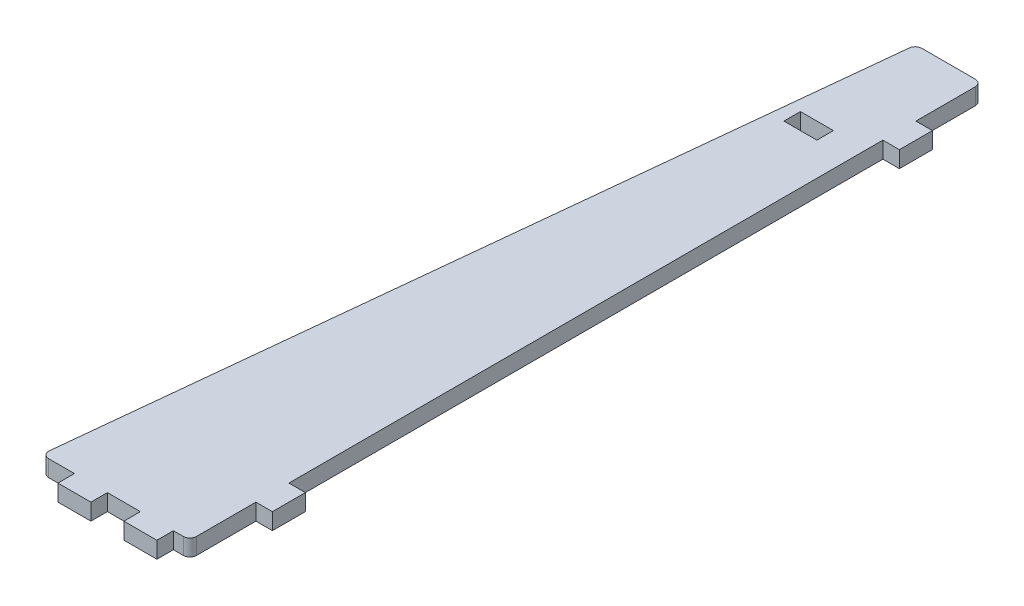
SolidWorks part; units mm, degrees
material "Beech"
ref_plane "Front Plane" through (0, 0, 0) normal (0, 0, 1) x (1, 0, 0)
ref_plane "Top Plane" through (0, 0, 0) normal (0, 1, 0) x (1, 0, 0)
ref_plane "Right Plane" through (0, 0, 0) normal (1, 0, 0) x (0, 0, -1)
sketch "Sketch1" plane through (0, 0, 0) normal (0, 1, 0) x (1, 0, 0)
  line L0 (0, 0) -> (12.7, 0)
  line L1 (12.7, 0) -> (12.7, -6.35)
  line L2 (12.7, -6.35) -> (25.4, -6.35)
  line L3 (25.4, -6.35) -> (25.4, 0)
  line L4 (25.4, 0) -> (38.1, 0)
  line L5 (38.1, 0) -> (38.1, -6.35)
  line L6 (38.1, -6.35) -> (50.8, -6.35)
  line L7 (50.8, -6.35) -> (50.8, 0)
  line L8 (50.8, 0) -> (57.15, 0)
  line L9 (57.15, 0) -> (57.15, 25.4)
  line L10 (57.15, 304.8) -> (31.75, 304.8)
  line L11 (31.75, 304.8) -> (0, 0)
  line L12 (57.15, 25.4) -> (63.5, 25.4)
  line L13 (63.5, 25.4) -> (63.5, 38.1)
  line L14 (63.5, 38.1) -> (57.15, 38.1)
  line L15 (57.15, 38.1) -> (57.15, 266.7)
  line L16 (57.15, 266.7) -> (63.5, 266.7)
  line L17 (63.5, 266.7) -> (63.5, 279.4)
  line L18 (63.5, 279.4) -> (57.15, 279.4)
  line L19 (57.15, 279.4) -> (57.15, 304.8)
  line L20 (31.75, 260.35) -> (31.75, 254)
  line L21 (31.75, 260.35) -> (44.45, 260.35)
  line L22 (31.75, 254) -> (44.45, 254)
  line L23 (44.45, 260.35) -> (44.45, 254)
  dimension "D1" = 12.7
  dimension "D2" = 6.35
  dimension "D3" = 25.4
  dimension "D4" = 25.4
  dimension "D5" = 12.7
  dimension "D6" = 304.8
  dimension "D7" = 25.4
  dimension "D8" = 25.4
  dimension "D9" = 6.35
  dimension "D10" = 254
  dimension "D11" = 6.35
  dimension "D12" = 12.7
  dimension "D13" = 12.7
extrude "Boss-Extrude1" add sketch "Sketch1" along normal blind 6.35
fillet "Fillet1" radius 2.54 4 edges at (57.15, 3.175, 0) (57.15, 3.175, -304.8) (31.75, 3.175, -304.8) (0, 3.175, 0)
equation "\"CageLeftBottomEdge\"=22.11mm"
equation "\"CageLeftTopEdge\"=22.11mm"
equation "\"CageRightBottomEdge\"=21.63mm"
equation "\"CageRightTopEdge\"=21.63mm"
equation "\"CageHeight\"=86.04mm"
equation "\"CageLength\"=73.76mm"
equation "\"CageTopScrewClearance\"=10mm"
equation "\"CageBottomScrewClearance\"=25mm"
equation "\"CageLeftTopDepth\"= 11.65mm"
equation "\"CageLeftBottomDepth\"=11.11mm"
equation "\"CageLeftTopHeight\"=8.56175mm"
equation "\"CageLeftBottomHeight\"=16mm"
equation "\"CageRightTopDepth\"= 11.05mm"
equation "\"CageRightBottomDepth\"=10.58mm"
equation "\"CageRightTopHeight\"=9.6mm"
equation "\"CageRightBottomHeight\"=15.49mm"
equation "\"CageLeftTopChannelDepth\"=2.41908mm"
equation "\"CageLeftBottomChannelDepth\"=2.588mm"
equation "\"CageLeftChannelHeight\"=11.7mm"
equation "\"CageRightTopChannelDepth\"=2.32mm"
equation "\"CageRightBottomChannelDepth\"=2.318mm"
equation "\"CageRightChannelHeight\"=10mm"
equation "\"CageChanRelHeight\"=23.99mm"
equation "\"CageChanRelDepth\"=5.492mm"
equation "\"CageChamberRadius\"=16.261mm"
equation "\"CageScrewDiameter\"=4.8mm"
equation "\"CageSetScrewDiameter\"=3.5mm"
equation "\"CageAxleRadius\"=6.639mm"
equation "\"CageAxleKeyHeight\"=1.619mm"
equation "\"CageAxleKeyWidth\"=2.662mm"
equation "\"CageHoseWindowWidth\"=16.29mm"
equation "\"CageHoseWindowHeight\"=26.5mm"
equation "\"CageHoseWindow-Edge\"=8.89mm"
equation "\"CageScrew-VerticalEdge\"=5.0mm"
equation "\"CageScrew-HorizontalEdge\"=7.5mm"
equation "\"CageScrew-HoseCornerScrewEdge\"=4.45mm"
equation "\"CageAxle-BottomEdge\"=56.05mm"
equation "\"CageAxle-FrontEdge\"=46.03mm"
equation "\"CageBackSetScrew-Axle\"=40mm"
equation "\"CageFrontSetScrew-Axle\"=22mm"
equation "\"CageVelocityWindow-BackEdge\"=34.8mm"
equation "\"CageVelocityWindow-BottomEdge\"=27.55mm"
equation "\"CageVelocityWindowHeight\"=22.29mm"
equation "\"CageVelocityWindowWidth\"=12.61mm"
equation "\"TriggerSlot-BottomEdge\"=6.35mm"
equation "\"TriggerSlot-FrontEdge\"=15mm"
equation "\"TriggerSlotSize\"=6.7mm"
equation "\"TriggerRackOffset\"=.236224in"
equation "\"TriggerSlotSizeInt\"=.25in"
equation "\"MotorMountLegLength\"=.25in"
equation "\"GearOffset\"=.264907in"
equation "\"TriggerSlotSpacing\"=.25in"
equation "\"TriggerMiniSlotWidth\"=3.5mm"
equation "\"TriggerRackWidth\"=6.5mm"
equation "\"TGMGearFaceDiameter\"=24.40mm"
equation "\"TGMCylinderLength\"=15.00mm"
equation "\"TGMScrewHole-Center\"=8.70mm"
equation "\"TGMScrewHoleDiameter\"=5.04mm"
equation "\"TGMCenterHoleDiameter\"=9.50mm"
equation "\"TGMShaftCollarSideLength\"=19.00mm"
equation "\"TGMShaftCollarDockingDepth\"=7.00mm"
equation "\"whitemotordepth\"=11.27mm"
equation "\"whitemotorbackdepth\"=3.845mm"
equation "\"whitemotoraxledepth\" = 3.5mm"
equation "\"whitemotoraxleoffset\"=11.4mm"
equation "\"whitemotorwidth\"=12.07mm"
equation "\"whitemotorheight\"=16.68mm"
equation "\"whitemotorcylinderlength\" =13.04mm"
equation "\"whitemotorcylinderradius\"=3.845mm"
equation "\"whitemotorcylinderoffset\"=2.35mm"
equation "\"whitemotorcutoutlength\"=1.88mm"
equation "\"whitemotorouterrad\"=5mm"
equation "\"whitemotorinnerrad\"=2.95mm"
equation "\"elasticracklength\"=2in"
equation "\"elasticrackpegsize\"=.25in"
equation "\"elasticrackpegbuffer\"=.125in"
equation "\"elasticrackpegspacing\"=1.76476378in"
equation "\"elasticbaybuffer\"=.25in"
equation "\"elasticdepth\"=.125in"
equation "\"elasticbaydepth\"=.75in"
equation "\"motormountwidth\"=12mm"
equation "\"motormountcornerfillet\"=3mm"
equation "\"pandiscradius\"=14in"
equation "\"towermaterialwidth\"=.25in"
equation "\"towerslotlength\"=.5in"
equation "\"towermarkerspace\"=5in"
equation "\"towerslothorizoffset\"=1in"
equation "\"towerslothorizspacing\"=2in"
equation "\"towerslotvertoffset\"=3in"
equation "\"D1@Sketch1\"=\"towerslotlength\""
equation "\"D2@Sketch1\"=\"towermaterialwidth\""
equation "\"towerupslot\"=1in"
equation "\"D3@Sketch1\"=\"towerupslot\""
equation "\"towerslotvertspacing\"=1in"
equation "\"D4@Sketch1\"=\"towerslotvertspacing\""
equation "\"D5@Sketch1\"=\"towerslotlength\""
equation "\"towerheight\"=12in"
equation "\"D6@Sketch1\"=\"towerheight\""
equation "\"D7@Sketch1\"=\"towerslotlength\"*2"
equation "\"D8@Sketch1\"=\"towerupslot\""
equation "\"D9@Sketch1\"=\"towerslotvertoffset\"-(\"towermarkerspace\"/2)-\"towermaterialwidth\""
equation "\"towermotorpanelheight\"=10in"
equation "\"D10@Sketch1\"=\"towermotorpanelheight\""
equation "\"D11@Sketch1\"=\"towermaterialwidth\""
equation "\"D12@Sketch1\"=\"towerslotlength\""
equation "\"D13@Sketch1\"=\"towerslotlength\""
equation "\"D1@Boss-Extrude1\"=\"towermaterialwidth\""
equation "\"toweraxle\"=.5in"
equation "\"towerplatslotoffset\"=1.5in"
equation "\"towerplatdepth\"=2in"
equation "\"stepperouterrad\"=10mm"
equation "\"stepperscrewsize\"=3.45mm"
equation "\"stepperscrewc2c\"=49.5mm"
equation "\"stepperdepthoffset\"=24mm"
equation "\"stepperhorizoffset\"=22.91mm"
equation "\"shaftslotOD\"=18.8mm"
equation "\"shaftslotID\"=13.28mm"
equation "\"shaftkeywidth\"=2.67mm"
equation "\"shaftkeydepth\"=1.8mm"
equation "\"shaftcollartotaldepth\"=12.5mm"
equation "\"shaftsquaredepth\"=6mm"
equation "\"shaftsetscrewsize\"=3.5mm"
equation "\"shaftkeytightdepth\"=1.85mm"
equation "\"shaftslottightID\"=12.78mm"
equation "\"shaftsetscrewoffset\"=9mm"
equation "\"cagecollartotaldepth\"=10mm"
equation "\"cagecollartotalwidth\"=35mm"
equation "\"cagecollarbasedepth\"=4mm"
equation "\"ajaxaxlesize\"=3.87mm"
equation "\"ajaxinnercut\"=2.3mm"
equation "\"ajaxwidth\"=6.1mm"
equation "\"ajaxdiametral\"=25.8854"
equation "\"ajax4020gap\"=29.5mm"
equation "\"ajax4010gap\"=24.5mm"
equation "\"ajaxhubdepth\"=.25in"
equation "\"ajaxcutoutdepth\"=2.3mm"
equation "\"ajax20hubbuffer\"=0.240157in"
equation "\"ajax20hubholeoffset\"=.19685in"
equation "\"ajax20hubholesize\"=.059055in"
equation "\"ajax20cutoutint\"=13.4mm"
equation "\"ajax40hubholesize\"=7.21mm"
equation "\"ajax40hubholeoffset\"=10mm"
equation "\"ajax40hubbuffer\"=.350394in"
equation "\"ajax40cutoutint\"=32.6mm"
equation "\"no6diam\"=.146in"
equation "\"shconangle\"=20deg"
equation "\"shconlen\"=1in"
equation "\"lnconlen\"=1.5in"
equation "\"lnconangle\"=15deg"
